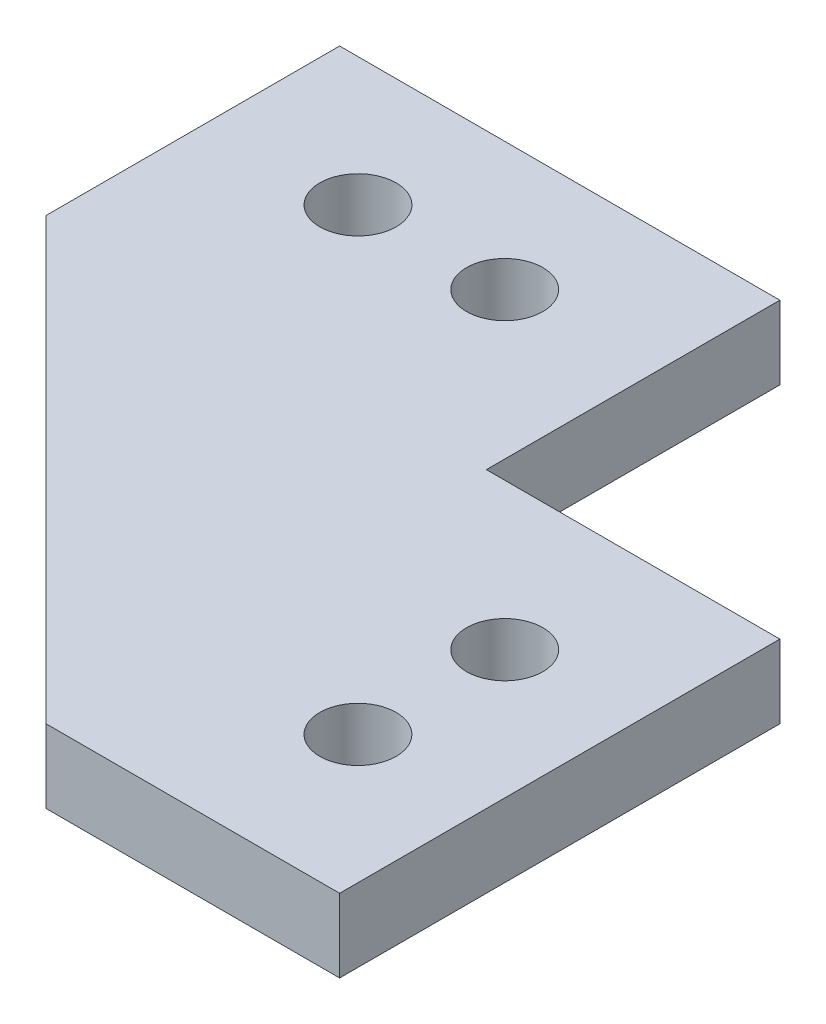
SolidWorks part; units mm, degrees
material "6061-T6 (SS)"
ref_plane "Front Plane" through (0, 0, 0) normal (0, 0, 1) x (1, 0, 0)
ref_plane "Top Plane" through (0, 0, 0) normal (0, 1, 0) x (1, 0, 0)
ref_plane "Right Plane" through (0, 0, 0) normal (1, 0, 0) x (0, 0, -1)
sketch "Sketch1" plane through (0, 0, 0) normal (0, 1, 0) x (1, 0, 0)
  line L0 (32.5438, 0) -> (32.5438, -19.05) construction
  line L5 (32.5438, -19.05) -> (32.5438, -25.4) construction
  line L7 (38.1, 0) -> (6.35, -31.75) construction
  line L8 (38.1, -12.7) -> (25.4, -12.7)
  line L9 (38.1, -31.75) -> (25.4, -31.75)
  line L10 (38.1, -12.7) -> (38.1, -31.75)
  line L11 (25.4, -31.75) -> (6.35, -12.7)
  line L12 (19.05, -5.5562) -> (12.7, -5.5563) construction
  line L13 (38.1, -5.5562) -> (19.05, -5.5562) construction
  line L14 (25.4, 0) -> (6.35, 0)
  line L15 (6.35, 0) -> (6.35, -12.7)
  line L16 (25.4, 0) -> (25.4, -12.7)
  circle A0 centre (32.5438, -19.05) radius 1.651
  circle A1 centre (32.5438, -25.4) radius 1.651
  circle A4 centre (12.7, -5.5563) radius 1.651
  circle A5 centre (19.05, -5.5562) radius 1.651
  point P5 (32.5438, 0)
  point P15 (38.1, -12.7)
  point P21 (15.875, -22.225)
  point P23 (25.4, 0)
  dimension "D5" = 3.302
  dimension "D7" = 3.302
  dimension "D1" = 12.7
  dimension "D2" = 19.05
  dimension "D3" = 5.5562
  dimension "D4" = 19.05
  dimension "D6" = 6.35
  dimension "D8" = 12.7
  dimension "D9" = 12.7
extrude "Boss-Extrude1" add sketch "Sketch1" along normal blind 3.175
